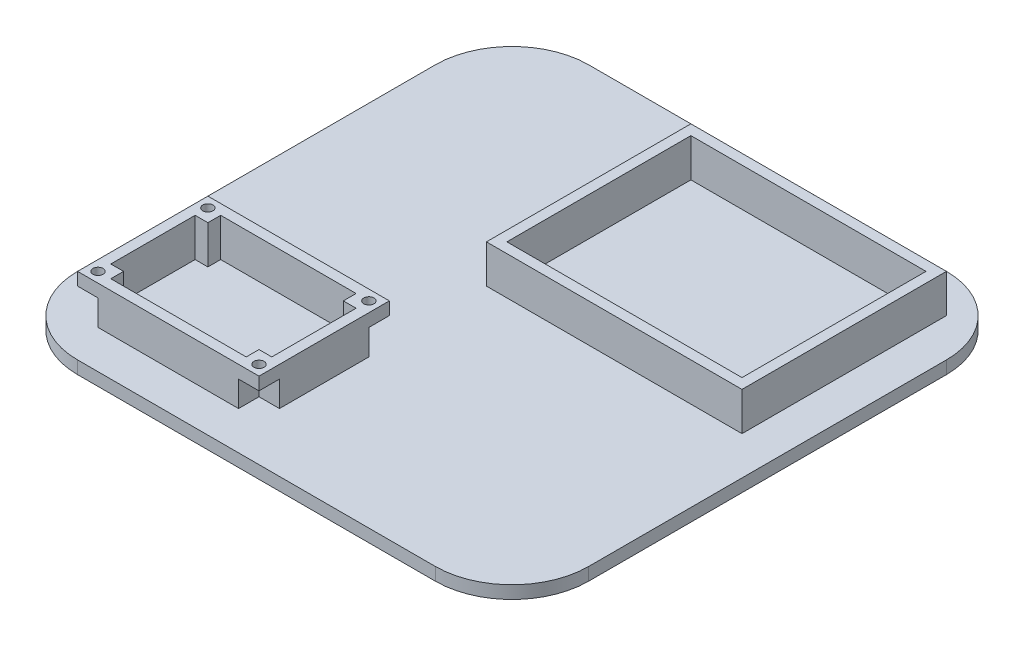
SolidWorks part; units mm, degrees
ref_plane "Front Plane" through (0, 0, 0) normal (0, 0, 1) x (1, 0, 0)
ref_plane "Top Plane" through (0, 0, 0) normal (0, 1, 0) x (1, 0, 0)
ref_plane "Right Plane" through (0, 0, 0) normal (1, 0, 0) x (0, 0, -1)
sketch "Sketch1" plane through (0, 0, 0) normal (0, 1, 0) x (1, 0, 0)
  line L1 (0, 0) -> (200, 0)
  line L2 (0, 0) -> (0, 200)
  line L3 (0, 200) -> (200, 200)
  line L4 (200, 0) -> (200, 200)
  dimension "D1" = 200
  dimension "D2" = 200
extrude "Boss-Extrude1" add sketch "Sketch1" along normal blind 5
sketch "Sketch4" plane through (0, 5, 0) normal (0, 1, 0) x (1, 0, 0)
  line L0 (200, 200) -> (0, 200) construction
  line L1 (85, 105) -> (185, 105)
  line L2 (85, 105) -> (85, 185)
  line L3 (85, 185) -> (185, 185)
  line L4 (185, 105) -> (185, 185)
  line L5 (200, 0) -> (200, 200) construction
  line L6 (227.6457, 185) -> (227.6457, 181) construction
  line L7 (89, 181) -> (181, 181)
  line L8 (89, 181) -> (89, 109)
  line L9 (89, 109) -> (181, 109)
  line L10 (181, 181) -> (181, 109)
  line L11 (225.2164, 109) -> (225.2164, 105) construction
  line L12 (85, 165.0446) -> (89, 165.0446) construction
  line L13 (181, 169.4051) -> (185, 169.4051) construction
  dimension "D1" = 100
  dimension "D2" = 72
  dimension "D3" = 15
  dimension "D4" = 15
  dimension "D5" = 92
extrude "Boss-Extrude2" add sketch "Sketch4" along normal blind 15
sketch "Sketch8" plane through (0, 5, 0) normal (0, 1, 0) x (1, 0, 0)
  line L0 (0, 0) -> (200, 0) construction
  line L1 (15, 15) -> (86, 15)
  line L2 (15, 15) -> (15, 66)
  line L3 (15, 66) -> (86, 66)
  line L4 (86, 15) -> (86, 66)
  line L9 (0, 200) -> (0, 0) construction
  line L10 (19, 57) -> (24, 57)
  line L15 (24, 57) -> (24, 62)
  line L16 (24, 62) -> (77, 62)
  line L17 (77, 62) -> (77, 57)
  line L18 (77, 57) -> (82, 57)
  line L19 (82, 57) -> (82, 24)
  line L20 (82, 24) -> (77, 24)
  line L21 (77, 24) -> (77, 19)
  line L22 (77, 19) -> (24, 19)
  line L23 (24, 19) -> (24, 24)
  line L24 (24, 24) -> (19, 24)
  line L25 (19, 57) -> (19, 24)
  circle A0 centre (19, 62) radius 2
  circle A1 centre (82, 62) radius 2
  circle A2 centre (82, 19) radius 2
  circle A3 centre (19, 19) radius 2
  dimension "D5" = 2
  dimension "D1" = 71
  dimension "D2" = 51
  dimension "D3" = 15
  dimension "D4" = 15
  dimension "D6" = 4
  dimension "D7" = 4
  dimension "D10" = 5
  dimension "D11" = 5
  dimension "D12" = 5
  dimension "D13" = 5
  dimension "D14" = 4
  dimension "D15" = 4
  dimension "D16" = 4
  dimension "D8" = 2
  dimension "D9" = 2
extrude "Boss-Extrude4" add sketch "Sketch8" along normal blind 15
sketch "Sketch9" plane through (0, 5, 0) normal (0, 1, 0) x (1, 0, 0)
  line L0 (15, 66) -> (15, 15) construction
  line L1 (15, 66) -> (23, 66)
  line L2 (15, 66) -> (15, 58)
  line L3 (15, 58) -> (23, 58)
  line L4 (23, 66) -> (23, 58)
  dimension "D1" = 8
extrude "Cut-Extrude11" cut sketch "Sketch9" along normal offset from surface (10 mm away) 5 up to face at (19, 20, -60)
pattern_linear "LPattern1" count 2 spacing 63 along (1, 0, 0) count 2 spacing 43 along (0, 0, 1) of "Cut-Extrude11"
fillet "Fillet1" radius 30 4 edges at (0, 2.5, 0) (200, 2.5, 0) (0, 2.5, -200) (200, 2.5, -200)
